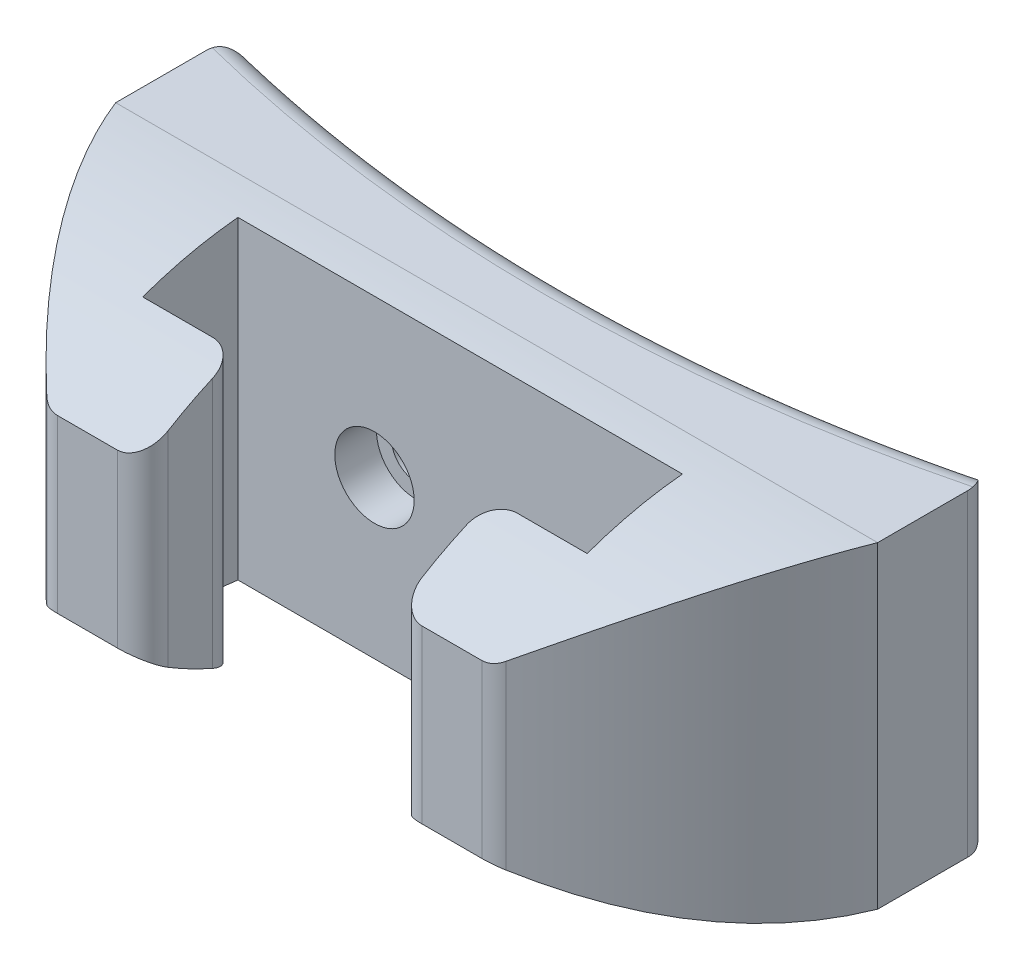
SolidWorks part; units mm, degrees
ref_plane "Front Plane" through (0, 0, 0) normal (0, 0, 1) x (1, 0, 0)
ref_plane "Top Plane" through (0, 0, 0) normal (0, 1, 0) x (1, 0, 0)
ref_plane "Right Plane" through (0, 0, 0) normal (1, 0, 0) x (0, 0, -1)
sketch "Sketch1" plane through (0, 0, 0) normal (0, 1, 0) x (1, 0, 0)
  line L1 (38.1, 15.875) -> (38.1, -19.05)
  line L2 (38.1, -19.05) -> (12.7, -19.05)
  line L3 (-12.7, -19.05) -> (-12.7, -9.525)
  line L4 (22.225, 0) -> (-22.225, 0)
  line L5 (-12.7, -9.525) -> (-22.225, -9.525)
  line L6 (-12.7, -19.05) -> (-38.1, -19.05)
  line L7 (-38.1, -19.05) -> (-38.1, 15.875)
  line L8 (-22.225, -9.525) -> (-22.225, 0)
  line L10 (22.225, 0) -> (22.225, -9.525)
  line L11 (22.225, -9.525) -> (12.7, -9.525)
  line L12 (12.7, -9.525) -> (12.7, -19.05)
  line L13 (0, 163.4357) -> (0, 0) construction
  arc A0 (-38.1, 15.875) -> (38.1, 15.875) centre (0, 163.4357) ccw
  point P5 (0, 0)
  dimension "D1" = 304.8
  dimension "D2" = 9.525
  dimension "D3" = 76.2
  dimension "D4" = 9.525
  dimension "D5" = 25.4
  dimension "D6" = 44.45
  dimension "D7" = 34.925
extrude "Boss-Extrude1" add sketch "Sketch1" along normal blind 31.75
hole_wizard "CBORE for #8 Socket Head Cap Screw1" positions "Sketch2" profile "Sketch3" counterbore size "#8" standard "ANSI Inch"
sketch "Sketch2" plane through (0, 0, 0) normal (0, 0, 1) x (1, 0, 0)
  line L0 (-8.5725, 15.875) -> (8.5725, 15.875) construction
  line L4 (0, 31.75) -> (0, 0)
  line L5 (-22.225, 31.75) -> (22.225, 31.75) construction
  point P0 (-8.5725, 15.875)
  point P2 (8.5725, 15.875)
  point P22 (0, 15.875)
  dimension "D1" = 17.145
sketch "Sketch3" plane through (-8.5725, 15.875, 0) normal (1, 0, 0) x (0, -1, 0)
  line L0 (0, 0) -> (0, 11.277)
  line L1 (0, 11.277) -> (2.4574, 11.277)
  line L3 (2.4574, 11.277) -> (2.4575, 4.1656)
  line L4 (2.4575, 4.1656) -> (3.9687, 4.1656)
  line L5 (3.9687, 4.1656) -> (3.9688, 0)
  line L7 (3.9688, 0) -> (0, 0)
  line L11 (0, -6.35) -> (0, 107.95) construction
  dimension "Thru Hole Dia." = 4.9149
  dimension "Thru Hole Depth" = 11.277
  dimension "C'Bore Dia." = 7.9375
  dimension "C'Bore Depth" = 4.1656
sketch "Sketch4" plane through (0, 31.75, 0) normal (0, 1, 0) x (1, 0, 0)
  line L0 (0, 0) -> (17.145, 25.4) construction
  line L1 (-22.225, 0) -> (22.225, 0) construction
  line L2 (17.145, 25.4) -> (0, 25.4) construction
  line L3 (0, 25.4) -> (0, 0) construction
  line L4 (-38.1, -19.05) -> (-38.1, 3.6495)
  line L5 (-38.1, 15.875) -> (-38.1, -19.05) construction
  line L6 (-22.216, -19.05) -> (-38.1, -19.05)
  arc A0 (-38.1, 3.6495) -> (-22.216, -19.05) centre (17.145, 25.4) ccw
  dimension "D1" = 17.145
  dimension "D3" = 118.745
  dimension "D2" = 25.4
extrude "Cut-Extrude1" cut sketch "Sketch4" against normal through all
mirror "Mirror1" about plane through (0, 0, 0) normal (1, 0, 0) of "Cut-Extrude1"
sketch "Sketch5" plane through (-38.1, 0, 0) normal (-1, 0, 0) x (0, 0, 1)
  line L0 (-3.6495, 31.75) -> (19.05, 31.75)
  line L1 (19.05, 24.4475) -> (19.05, 7.3025)
  line L2 (19.05, 0) -> (19.05, 31.75) construction
  line L3 (19.05, 31.75) -> (19.05, 24.4475)
  line L4 (19.05, 7.3025) -> (19.05, 0)
  line L5 (19.05, 0) -> (-3.6495, 0)
  arc A0 (-3.6495, 31.75) -> (19.05, 24.4475) centre (-3.6495, -7.1815) cw
  arc A1 (19.05, 7.3025) -> (-3.6495, 0) centre (-3.6495, 38.9315) cw
  dimension "D1" = 17.145
extrude "Cut-Extrude3" cut sketch "Sketch5" against normal through all contours L0 A0 L3 | A1 L5 L4
fillet "Fillet1" radius 2.54 4 edges at (38.1, 15.875, -15.875) (-38.1, 15.875, -15.875) (0, 0, -11.0357) (0, 31.75, -11.0357)
fillet "Fillet2" radius 2.54 4 edges at (12.7, 15.875, 19.05) (-12.7, 15.875, 19.05) (-12.7, 15.875, 9.525) (12.7, 15.875, 9.525)
fillet "Fillet3" radius 2.54 2 edges at (22.216, 15.875, 19.05) (-22.216, 15.875, 19.05)
